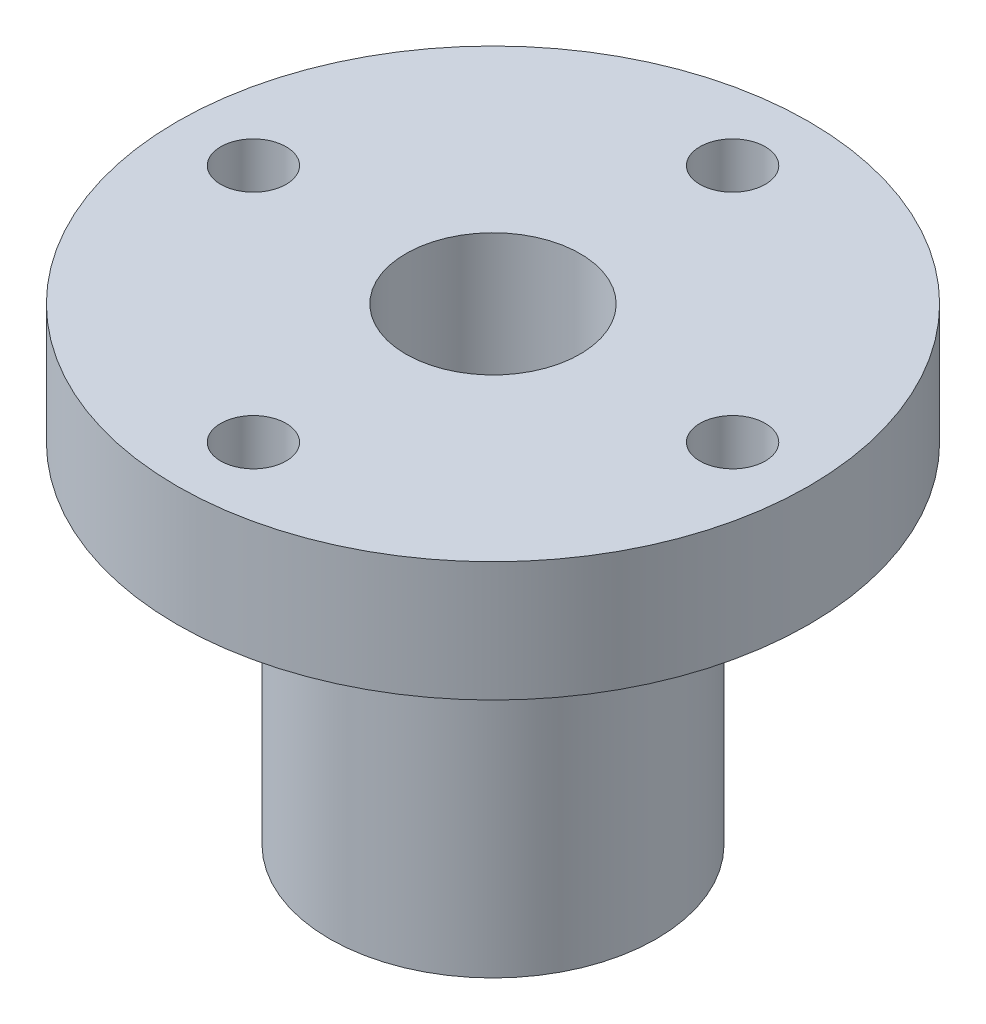
SolidWorks part; units mm, degrees
ref_plane "Front Plane" through (0, 0, 0) normal (0, 0, 1) x (1, 0, 0)
ref_plane "Top Plane" through (0, 0, 0) normal (0, 1, 0) x (1, 0, 0)
ref_plane "Right Plane" through (0, 0, 0) normal (1, 0, 0) x (0, 0, -1)
sketch "Sketch1" plane through (0, 0, 0) normal (0, 1, 0) x (1, 0, 0)
  circle A0 centre (0, 0) radius 7.5
  circle A1 centre (0, 0) radius 4
  dimension "D1" = 15
  dimension "D2" = 8
extrude "Boss-Extrude1" add sketch "Sketch1" along normal blind 16
sketch "Sketch2" plane through (0, 16, 0) normal (0, 1, 0) x (1, 0, 0)
  circle A0 centre (0, 0) radius 7.5 construction
  circle A1 centre (0, 0) radius 4 construction
  circle A2 centre (0, 0) radius 7.5
  circle A3 centre (0, 0) radius 4
  circle A4 centre (0, 0) radius 14.5
  circle M1 centre (0, 0) radius 7.5
  dimension "D1" = 29
extrude "Boss-Extrude2" add sketch "Sketch2" along normal blind 5.5 separate body contours A4 M1
sketch "Sketch3" plane through (0, 16, 0) normal (0, 1, 0) x (1, 0, 0)
  circle A1 centre (0, 0) radius 4
  circle A2 centre (0, 0) radius 4
  circle A3 centre (0, 0) radius 7.5
  circle A4 centre (0, 0) radius 7.5
  dimension "D1" = 0
  dimension "D2" = 0
extrude "Boss-Extrude3" add sketch "Sketch3" along normal blind 5.5
sketch "Sketch4" plane through (0, 21.5, 0) normal (0, 1, 0) x (1, 0, 0)
  line L0 (0, 12.5) -> (0, -12.5)
  circle A0 centre (0, -11) radius 1.5
  circle A1 centre (-27.0053, 2.2823) radius 1.5
  circle A2 centre (0, 11) radius 1.5
  circle A3 centre (-25.7791, 0) radius 1.5
  circle A4 centre (11, 0) radius 1.5
  circle A5 centre (0, -11) radius 1.5
  circle A6 centre (-11, 0) radius 1.5
  point P5 (0, 0)
  point P12 (0, 12.5)
  point P13 (0, -9.5)
  point P14 (0, -12.5)
  point P20 (12.5, 0)
  point P23 (0, -12.5)
  point P26 (-12.5, 0)
  point P27 (0, 0)
  dimension "D2" = 3
  dimension "D1" = 25
  dimension "D3" = 4
extrude "Cut-Extrude1" cut sketch "Sketch4" against normal blind 5.5 contours A4 | L0 A0 | L0 A0 | A6 | L0 A2 | L0 A2
